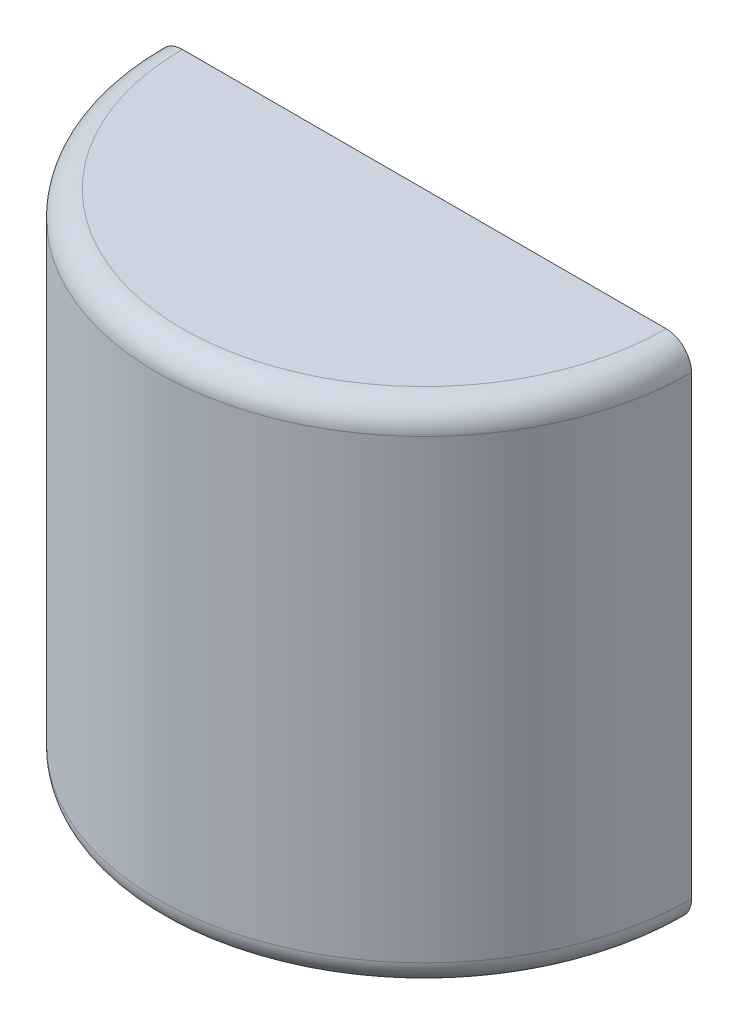
SolidWorks part; units mm, degrees
material "Custom Plastic"
ref_plane "Front Plane" through (0, 0, 0) normal (0, 0, 1) x (1, 0, 0)
ref_plane "Top Plane" through (0, 0, 0) normal (0, 1, 0) x (1, 0, 0)
ref_plane "Right Plane" through (0, 0, 0) normal (1, 0, 0) x (0, 0, -1)
sketch "Sketch1" plane through (0, 0, 0) normal (0, 0, 1) x (1, 0, 0)
  line L0 (0, 0) -> (0, 254) construction
  line L2 (0, 0) -> (-133.985, 0)
  line L3 (0, 0) -> (0, 254)
  line L4 (0, 254) -> (-133.985, 254)
  line L5 (-133.985, 0) -> (-133.985, 254)
  dimension "D1" = 254
  dimension "D2" = 133.985
revolve "Revolve1" add sketch "Sketch1" angle 180 about L0
fillet "Fillet1" radius 12.7 2 edges at (0, 0, 133.985) (0, 254, 133.985)
